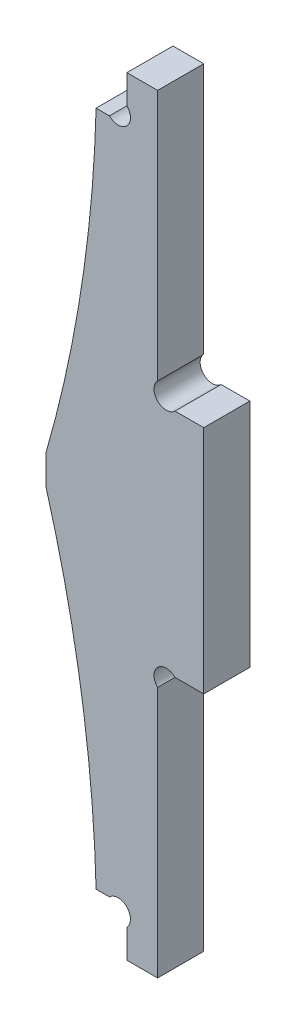
SolidWorks part; units mm, degrees
ref_plane "Plan de face" through (0, 0, 0) normal (0, 0, 1) x (1, 0, 0)
ref_plane "Plan de dessus" through (0, 0, 0) normal (0, 1, 0) x (1, 0, 0)
ref_plane "Plan de droite" through (0, 0, 0) normal (1, 0, 0) x (0, 0, -1)
sketch "Esquisse1" plane through (0, 0, 0) normal (0, 0, 1) x (1, 0, 0)
  line L0 (15.4045, 0) -> (-85.5542, 0) construction
  line L1 (0, -18.8409) -> (0, 122.638) construction
  line L2 (18.2726, 100) -> (-91.8341, 100) construction
  line L3 (-14.5, 128.6488) -> (-14.5, -16.4299) construction
  line L4 (12.5351, 50) -> (-47.846, 50) construction
  line L5 (-17.4432, 6) -> (9.0066, 6) construction
  line L6 (-4, -2.0364) -> (-4, 9.3368) construction
  line L7 (-8, 20.6393) -> (-8, 3.7809) construction
  line L8 (-20.8525, 48) -> (-6.4873, 48) construction
  line L9 (-4, 6) -> (-8.8783, 1.1217) construction
  line L10 (-14.5, 52) -> (-14.5, 48)
  line L11 (-8, 6) -> (-6.2627, 6)
  line L12 (-4, 3.7373) -> (-4, 0)
  line L13 (-4, 0) -> (0, 0)
  line L14 (6, 71.3281) -> (6, 33.5955) construction
  line L15 (7.0618, 35) -> (-2.6933, 35) construction
  line L16 (0, 35) -> (7.5769, 27.4231) construction
  line L17 (2.2627, 35) -> (6, 35)
  line L18 (-8, 94) -> (-6.2627, 94)
  line L19 (-4, 96.2627) -> (-4, 100)
  line L20 (0, 32.7373) -> (0, 0)
  line L21 (-4, 100) -> (0, 100)
  line L22 (0, 67.2627) -> (0, 100)
  line L23 (2.2627, 65) -> (6, 65)
  line L24 (6, 65) -> (6, 35)
  arc A0 (-4, 3.7373) -> (-6.2627, 6) centre (-5.1314, 4.8686) ccw
  arc A1 (-14.5, 48) -> (-8, 6) centre (-176.3878, 1.443) cw
  arc A2 (2.2627, 35) -> (0, 32.7373) centre (1.1314, 33.8686) ccw
  arc A3 (-14.5, 52) -> (-8, 94) centre (-176.3878, 98.557) ccw
  arc A4 (-4, 96.2627) -> (-6.2627, 94) centre (-5.1314, 95.1314) cw
  arc A5 (2.2627, 65) -> (0, 67.2627) centre (1.1314, 66.1314) cw
  point P26 (-14.5, 50)
  dimension "D6" = 15
  dimension "D1" = 2
  dimension "D2" = 4
  dimension "D3" = 8
  dimension "D4" = 6
  dimension "D5" = 45
  dimension "D7" = 6
  dimension "D8" = 45
extrude "Extrusion1" add sketch "Esquisse1" along normal blind 6
